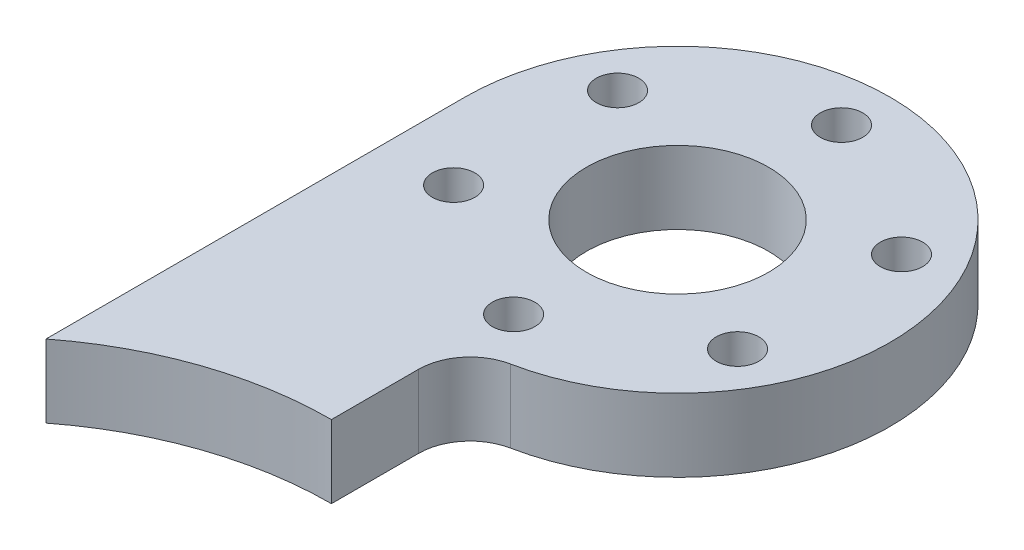
SolidWorks part; units mm, degrees
ref_plane "前视基准面" through (0, 0, 0) normal (0, 0, 1) x (1, 0, 0)
ref_plane "上视基准面" through (0, 0, 0) normal (0, 1, 0) x (1, 0, 0)
ref_plane "右视基准面" through (0, 0, 0) normal (1, 0, 0) x (0, 0, -1)
sketch "草图1" plane through (0, 0, 0) normal (0, 1, 0) x (1, 0, 0)
  line L1 (0, 0) -> (0, -57) construction
  line L6 (-17.5, -34.5056) -> (-17.5, 0)
  line L7 (0, -17.5) -> (0, -28.5)
  arc A1 (0, -28.5) -> (-17.5, -34.5056) centre (0, -57) ccw
  circle A2 centre (0, 0) radius 13.5 construction
  circle A3 centre (0, 13.5) radius 1.75
  circle A4 centre (11.6913, 6.75) radius 1.75
  circle A5 centre (11.6913, -6.75) radius 1.75
  circle A6 centre (0, -13.5) radius 1.75
  circle A7 centre (-11.6913, -6.75) radius 1.75
  circle A8 centre (-11.6913, 6.75) radius 1.75
  arc A9 (17.5, 0) -> (-17.5, 0) centre (0, 0) ccw
  arc A11 (0, -17.5) -> (17.5, 0) centre (0, 0) ccw
  point P26 (0, 0)
  dimension "D1" = 17.5
  dimension "D3" = 57
  dimension "D6" = 27
  dimension "D7" = 3.5
  dimension "D4" = 57
  dimension "D8" = 6
extrude "凸台-拉伸1" add sketch "草图1" along normal blind 6
fillet "圆角2" radius 4.25 1 edges at (0, 3, 17.5)
sketch "草图2" plane through (0, 6, 0) normal (0, 1, 0) x (1, 0, 0)
  circle A0 centre (0, 0) radius 7.5
  dimension "D1" = 15
extrude "切除-拉伸1" cut sketch "草图2" against normal blind 10
